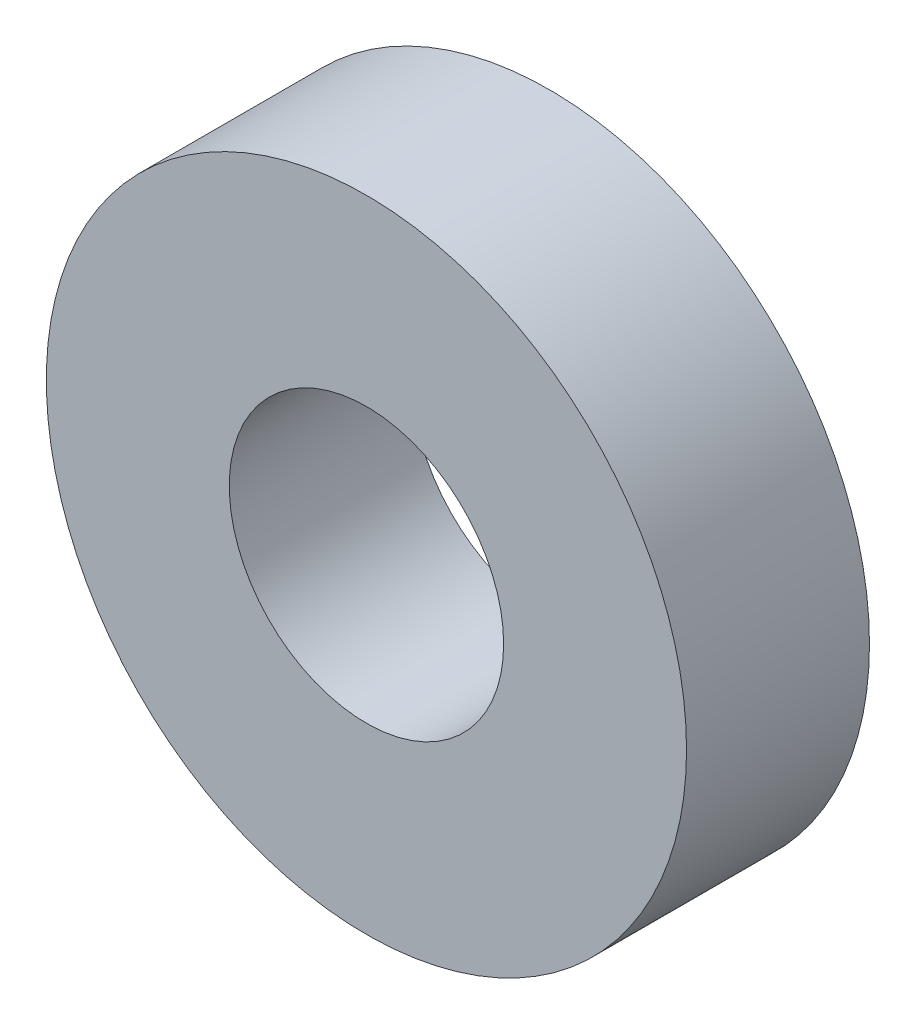
SolidWorks part; units mm, degrees
ref_plane "Front Plane" through (0, 0, 0) normal (0, 0, 1) x (1, 0, 0)
ref_plane "Top Plane" through (0, 0, 0) normal (0, 1, 0) x (1, 0, 0)
ref_plane "Right Plane" through (0, 0, 0) normal (1, 0, 0) x (0, 0, -1)
sketch "Sketch1" plane through (0, 0, 0) normal (0, 0, 1) x (1, 0, 0)
  circle A0 centre (0, 0) radius 14
  circle A1 centre (0, 0) radius 6
  dimension "D1" = 28
  dimension "D2" = 12
extrude "Boss-Extrude1" add sketch "Sketch1" along normal blind 8
